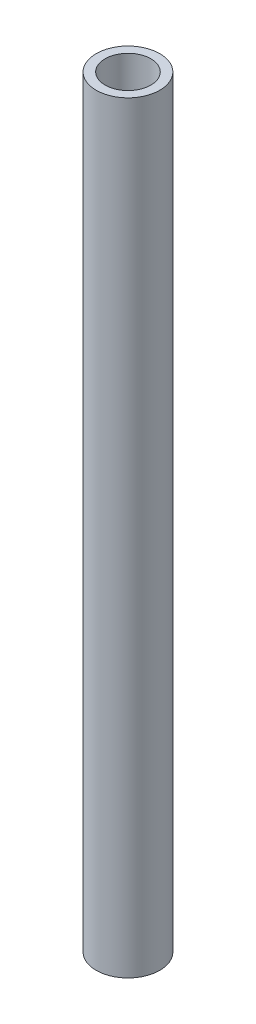
SolidWorks part; units mm, degrees
material "AISI 316 Stainless Steel Sheet (SS)"
ref_plane "Front Plane" through (0, 0, 0) normal (0, 0, 1) x (1, 0, 0)
ref_plane "Top Plane" through (0, 0, 0) normal (0, 1, 0) x (1, 0, 0)
ref_plane "Right Plane" through (0, 0, 0) normal (1, 0, 0) x (0, 0, -1)
sketch "Sketch1" plane through (0, 0, 0) normal (0, 1, 0) x (1, 0, 0)
  circle A0 centre (0, 0) radius 3.175
  circle A1 centre (0, 0) radius 2.286
  dimension "D1" = 6.35
  dimension "D2" = 4.572
extrude "Boss-Extrude1" add sketch "Sketch1" along normal blind 76.2
